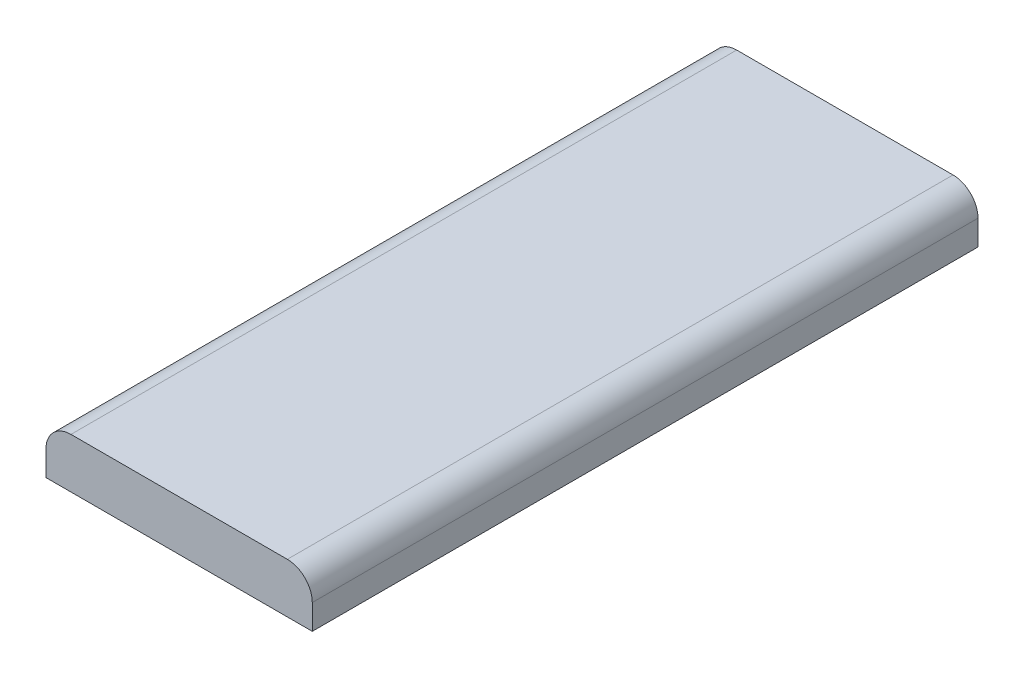
SolidWorks part; units mm, degrees
material "Corrugated Paper"
ref_plane "Front Plane" through (0, 0, 0) normal (0, 0, 1) x (1, 0, 0)
ref_plane "Top Plane" through (0, 0, 0) normal (0, 1, 0) x (1, 0, 0)
ref_plane "Right Plane" through (0, 0, 0) normal (1, 0, 0) x (0, 0, -1)
sketch "Sketch1" plane through (0, 0, 0) normal (0, 1, 0) x (1, 0, 0)
  line L1 (-10, 25) -> (10, 25)
  line L2 (-10, 25) -> (-10, -25)
  line L3 (-10, -25) -> (10, -25)
  line L4 (10, 25) -> (10, -25)
  line L5 (-10, 25) -> (10, -25) construction
  line L6 (-10, -25) -> (10, 25) construction
  point P0 (0, 0)
  dimension "D1" = 20
  dimension "D2" = 50
extrude "Boss-Extrude1" add sketch "Sketch1" along normal blind 3.75
fillet "Fillet1" radius 1.875 2 edges at (-10, 3.75, 0) (10, 3.75, 0)
